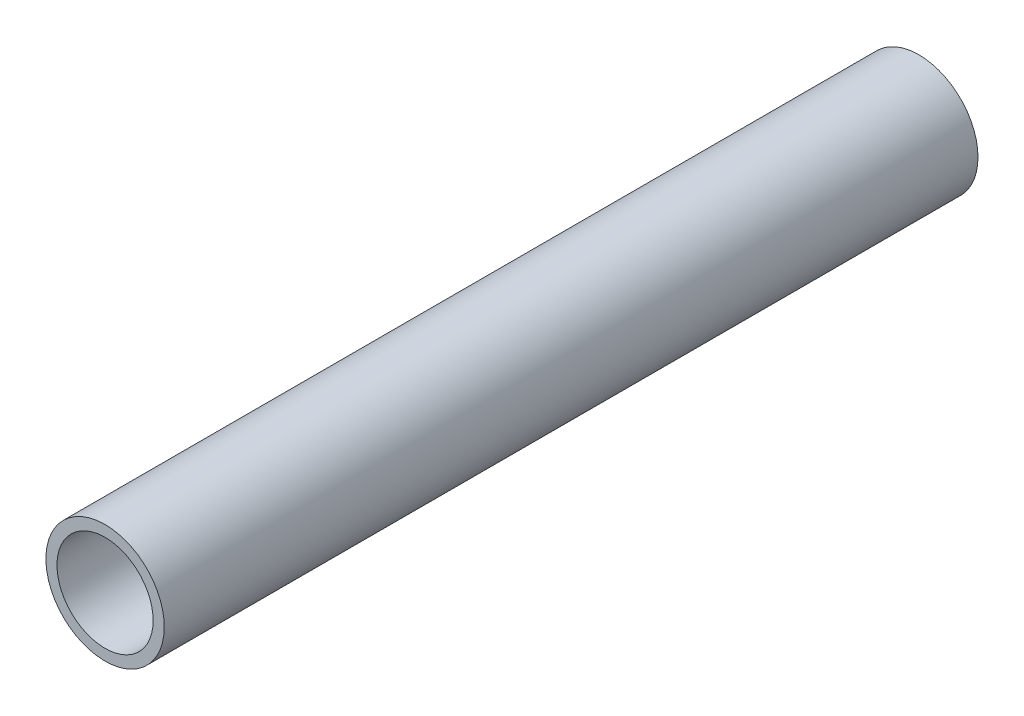
SolidWorks part; units mm, degrees
ref_plane "Alzado" through (0, 0, 0) normal (0, 0, 1) x (1, 0, 0)
ref_plane "Planta" through (0, 0, 0) normal (0, 1, 0) x (1, 0, 0)
ref_plane "Vista lateral" through (0, 0, 0) normal (1, 0, 0) x (0, 0, -1)
sketch "Croquis1" plane through (0, 0, 0) normal (0, 0, 1) x (1, 0, 0)
  circle A0 centre (0, 0) radius 4
  circle A1 centre (0, 0) radius 3.25
  dimension "D1" = 6.5
  dimension "D2" = 8
extrude "Saliente-Extruir1" add sketch "Croquis1" along normal blind 55
